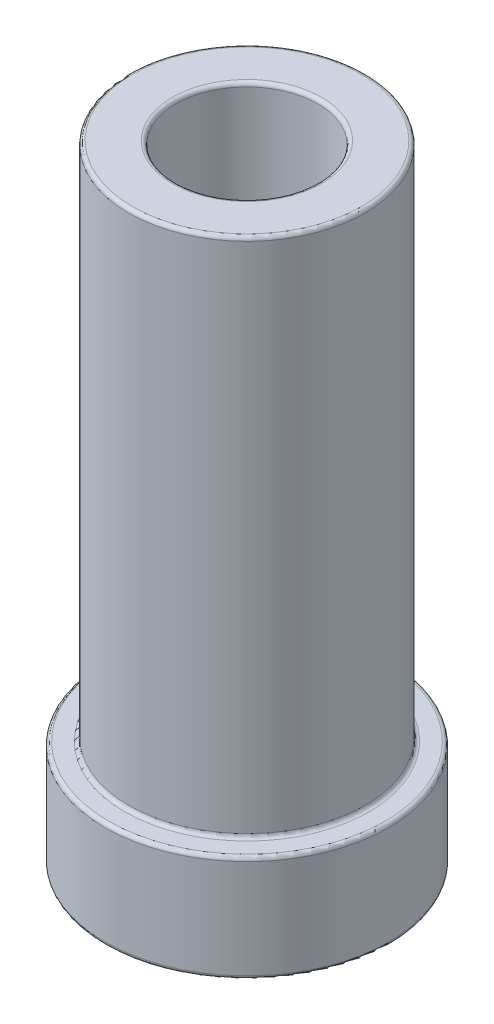
SolidWorks part; units mm, degrees
material "Aluminum Bronze"
ref_plane "Front Plane" through (0, 0, 0) normal (0, 0, 1) x (1, 0, 0)
ref_plane "Top Plane" through (0, 0, 0) normal (0, 1, 0) x (1, 0, 0)
ref_plane "Right Plane" through (0, 0, 0) normal (1, 0, 0) x (0, 0, -1)
sketch "Sketch1" plane through (0, 0, 0) normal (0, 1, 0) x (1, 0, 0)
  circle A0 centre (0, 0) radius 4.7625
  circle A1 centre (0, 0) radius 2.3813
  dimension "D1" = 9.525
  dimension "D2" = 4.7625
extrude "Boss-Extrude1" add sketch "Sketch1" along normal blind 3.5719
sketch "Sketch2" plane through (0, 3.5719, 0) normal (0, 1, 0) x (1, 0, 0)
  circle A0 centre (0, 0) radius 3.9688
  circle A1 centre (0, 0) radius 2.3813
  dimension "D1" = 7.9375
  dimension "D2" = 4.7625
extrude "Boss-Extrude2" add sketch "Sketch2" along normal blind 17.4625
fillet "Fillet1" radius 0.127 6 edges at (0, 21.0344, 2.3813) (0, 21.0344, 3.9688) (0, 3.5719, 4.7625) (0, 3.5719, 3.9688) (0, 0, 2.3813) (0, 0, 4.7625)
